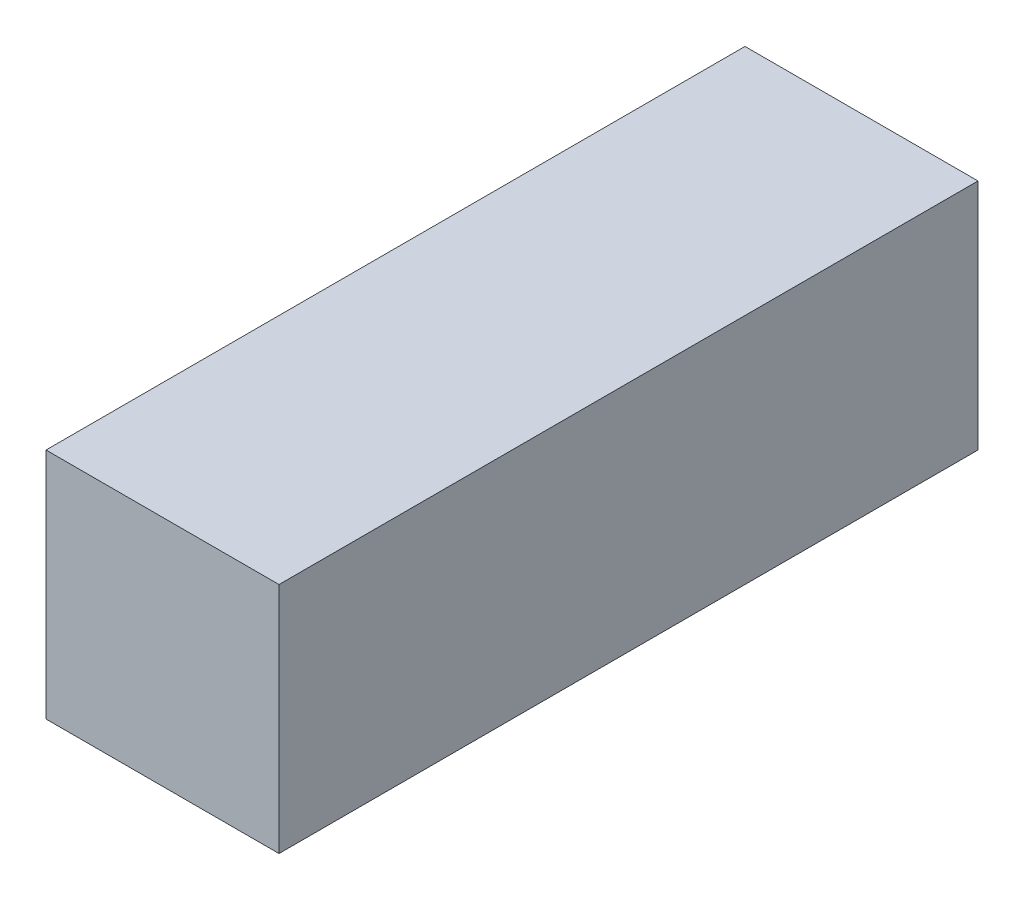
SolidWorks part; units mm, degrees
ref_plane "Front Plane" through (0, 0, 0) normal (0, 0, 1) x (1, 0, 0)
ref_plane "Top Plane" through (0, 0, 0) normal (0, 1, 0) x (1, 0, 0)
ref_plane "Right Plane" through (0, 0, 0) normal (1, 0, 0) x (0, 0, -1)
sketch "Sketch2" plane through (0, 0, 0) normal (0, 0, 1) x (1, 0, 0)
  line L1 (-1.5875, -1.5875) -> (1.5875, -1.5875)
  line L2 (-1.5875, -1.5875) -> (-1.5875, 1.5875)
  line L3 (-1.5875, 1.5875) -> (1.5875, 1.5875)
  line L4 (1.5875, -1.5875) -> (1.5875, 1.5875)
  line L5 (-1.5875, -1.5875) -> (1.5875, 1.5875) construction
  line L6 (-1.5875, 1.5875) -> (1.5875, -1.5875) construction
  point P0 (0, 0)
  dimension "D1" = 3.175
  dimension "D2" = 3.175
extrude "Boss-Extrude1" add sketch "Sketch2" along normal blind 9.525
